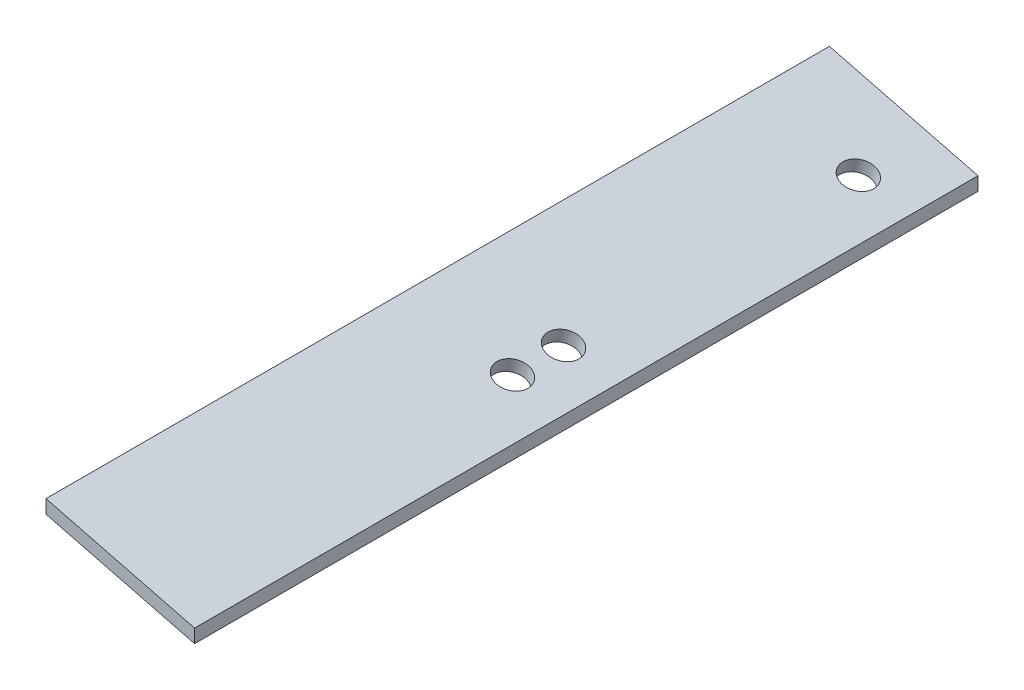
SolidWorks part; units mm, degrees
ref_plane "Plan de face" through (0, 0, 0) normal (0, 0, 1) x (1, 0, 0)
ref_plane "Plan de dessus" through (0, 0, 0) normal (0, 1, 0) x (1, 0, 0)
ref_plane "Plan de droite" through (0, 0, 0) normal (1, 0, 0) x (0, 0, -1)
sketch "Esquisse1" plane through (0, 0, 0) normal (0, 0, 1) x (1, 0, 0)
  line L0 (120, 155) -> (10, 183)
  line L1 (10, 183) -> (10, 173)
  line L2 (10, 183) -> (10, 0) construction
  line L3 (10, 173) -> (120, 145)
  line L4 (120, 0) -> (120, 155) construction
  line L5 (120, 145) -> (120, 155)
  dimension "D1" = 10
extrude "Boss.-Extru.1" add sketch "Esquisse1" against normal blind 580
sketch "Esquisse2" plane through (44.3558, 174.2549, 0) normal (0.2467, 0.9691, 0) x (0.9691, -0.2467, 0)
  circle A0 centre (41.3444, 308.7459) radius 11.8
  circle A1 centre (41.3444, 270.947) radius 11.8
  circle A2 centre (41.3444, 527) radius 11.8
extrude "Enlèv. mat.-Extru.1" cut sketch "Esquisse2" against normal blind 10
